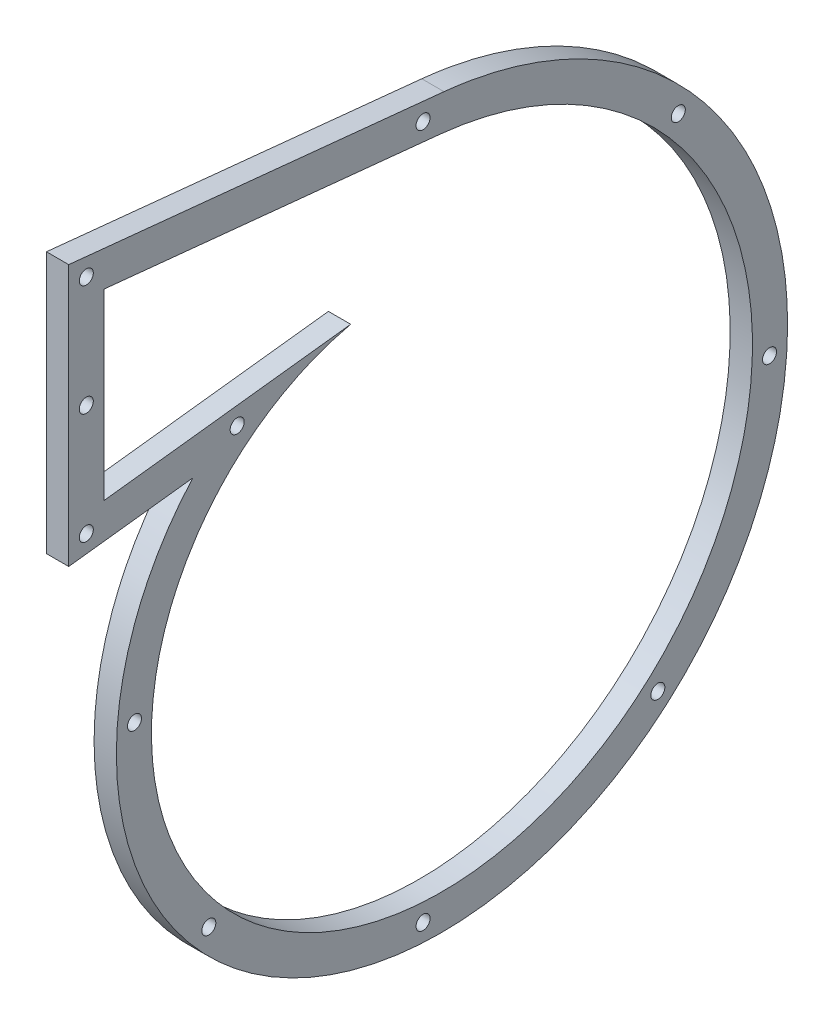
SolidWorks part; units mm, degrees
ref_plane "Front Plane" through (0, 0, 0) normal (0, 0, 1) x (1, 0, 0)
ref_plane "Top Plane" through (0, 0, 0) normal (0, 1, 0) x (1, 0, 0)
ref_plane "Right Plane" through (0, 0, 0) normal (1, 0, 0) x (0, 0, -1)
sketch "Sketch8" plane through (0, 0, 0) normal (1, 0, 0) x (0, 0, -1)
  line L0 (-42.4775, -245.3976) -> (306.8559, -245.3976) construction
  line L1 (-69, 0) -> (69, 0) construction
  circle A0 centre (0, 0) radius 69 construction
  point P15 (-130.5969, 140.8094)
  dimension "D1" = 138
sketch "Sketch4" plane through (0, 0, 0) normal (1, 0, 0) x (0, 0, -1)
  circle A0 centre (0, 0) radius 70.5
  dimension "D1" = 141
curve "Helix/Spiral1"
sketch "Sketch10" plane through (0, 0, 0) normal (1, 0, 0) x (0, 0, -1)
  line L0 (-20.6122, 67.4195) -> (-90.9357, 59.067)
  line L1 (-90.9357, 59.067) -> (-90.9357, 111.2319)
  line L2 (-90.9357, 111.2319) -> (4.9673, 101.5636)
  line L3 (-65.5693, 52.0095) -> (-100.9357, 47.809)
  line L4 (-100.9357, 47.809) -> (-100.9357, 122.2908)
  line L5 (-100.9357, 122.2908) -> (5.9703, 111.5132)
  line L6 (-95.9357, 116.7613) -> (5.4688, 106.5384) construction
  line L7 (-50.784, 58.8008) -> (-95.9357, 53.438) construction
  line L8 (-95.9357, 53.438) -> (-95.9357, 116.7613) construction
  spline S0 degree 3 poles (-1473.523, -1263.5766) (345.358, -198.0387) (91.6406, 117.3978) (-37.2156, 61.5605) (-41.1456, 59.4055) (-48.5847, 54.3658) (-52.0936, 51.4811) (-58.5545, 45.0647) (-61.5064, 41.533) (-66.7338, 33.9308) (-69.0091, 29.8604) (-72.7852, 21.311) (-74.2858, 16.8321) (-76.4391, 7.6138) (-77.0917, 2.8745) (-77.5044, -6.7034) (-77.2643, -11.5418) (-75.8778, -21.1493) (-74.7312, -25.9181) (-71.5495, -35.2161) (-69.5143, -39.7451) (-64.6057, -48.3972) (-61.7322, -52.5202) (-55.2279, -60.2051) (-51.5972, -63.7667) (-43.6886, -70.1896) (-39.4108, -73.0506) (-30.3435, -77.9547) (-25.5542, -79.9976) (-15.621, -83.1743) (-10.4772, -84.3079) (-0.0081, -85.6048) (5.317, -85.7681) (15.9653, -85.0965) (21.2883, -84.2616) (31.7447, -81.6003) (36.878, -79.774) (46.77, -75.1721) (51.5286, -72.3965) (60.4956, -65.9727) (64.7037, -62.3246) (72.4098, -54.265) (75.9074, -49.8536) (82.0541, -40.406) (84.7029, -35.3699) (89.0406, -24.8366) (90.7293, -19.3395) (93.067, -8.0675) (93.7159, -2.2928) (93.9294, 9.3374) (93.494, 15.1928) (91.5315, 26.7803) (90.0045, 32.5123) (85.8901, 43.6496) (83.3027, 49.0546) (77.1367, 59.3415) (73.5582, 64.2232) (65.5155, 73.2817) (61.0515, 77.4583) (51.3765, 84.9462) (46.1658, 88.2572) (35.1654, 93.8808) (29.376, 96.1932) (-135.5849, 144.7956) (-431.1519, -196.4432) (1091.6477, -1521.9747) knots -0.92756 -0.92756 -0.92756 -0.92756 0.03125 0.03125 0.0625 0.0625 0.09375 0.09375 0.125 0.125 0.15625 0.15625 0.1875 0.1875 0.21875 0.21875 0.25 0.25 0.28125 0.28125 0.3125 0.3125 0.34375 0.34375 0.375 0.375 0.40625 0.40625 0.4375 0.4375 0.46875 0.46875 0.5 0.5 0.53125 0.53125 0.5625 0.5625 0.59375 0.59375 0.625 0.625 0.65625 0.65625 0.6875 0.6875 0.71875 0.71875 0.75 0.75 0.78125 0.78125 0.8125 0.8125 0.84375 0.84375 0.875 0.875 0.90625 0.90625 0.9375 0.9375 0.96875 0.96875 1.799093 1.799093 1.799093 1.799093 only from (-20.6122, 67.4195) to (4.9673, 101.5636) construction
  spline S1 degree 3 poles (-20.6122, 67.4195) (-24.8771, 66.4553) (-29.0812, 65.0854) (-37.2156, 61.5605) (-41.1456, 59.4055) (-48.5847, 54.3658) (-52.0936, 51.4811) (-58.5545, 45.0647) (-61.5064, 41.533) (-66.7338, 33.9308) (-69.0091, 29.8604) (-72.7852, 21.311) (-74.2858, 16.8321) (-76.4391, 7.6138) (-77.0917, 2.8745) (-77.5044, -6.7034) (-77.2643, -11.5418) (-75.8778, -21.1493) (-74.7312, -25.9181) (-71.5495, -35.2161) (-69.5143, -39.7451) (-64.6057, -48.3972) (-61.7322, -52.5202) (-55.2279, -60.2051) (-51.5972, -63.7667) (-43.6886, -70.1896) (-39.4108, -73.0506) (-30.3435, -77.9547) (-25.5542, -79.9976) (-15.621, -83.1743) (-10.4772, -84.3079) (-0.0081, -85.6048) (5.317, -85.7681) (15.9653, -85.0965) (21.2883, -84.2616) (31.7447, -81.6003) (36.878, -79.774) (46.77, -75.1721) (51.5286, -72.3965) (60.4956, -65.9727) (64.7037, -62.3246) (72.4098, -54.265) (75.9074, -49.8536) (82.0541, -40.406) (84.7029, -35.3699) (89.0406, -24.8366) (90.7293, -19.3395) (93.067, -8.0675) (93.7159, -2.2928) (93.9294, 9.3374) (93.494, 15.1928) (91.5315, 26.7803) (90.0045, 32.5123) (85.8901, 43.6496) (83.3027, 49.0546) (77.1367, 59.3415) (73.5582, 64.2232) (65.5155, 73.2817) (61.0515, 77.4583) (51.3765, 84.9462) (46.1658, 88.2572) (35.1654, 93.8808) (29.376, 96.1932) (17.4097, 99.7188) (11.2331, 100.9319) (4.9673, 101.5636) knots 0 0 0 0 0.03125 0.03125 0.0625 0.0625 0.09375 0.09375 0.125 0.125 0.15625 0.15625 0.1875 0.1875 0.21875 0.21875 0.25 0.25 0.28125 0.28125 0.3125 0.3125 0.34375 0.34375 0.375 0.375 0.40625 0.40625 0.4375 0.4375 0.46875 0.46875 0.5 0.5 0.53125 0.53125 0.5625 0.5625 0.59375 0.59375 0.625 0.625 0.65625 0.65625 0.6875 0.6875 0.71875 0.71875 0.75 0.75 0.78125 0.78125 0.8125 0.8125 0.84375 0.84375 0.875 0.875 0.90625 0.90625 0.9375 0.9375 0.96875 0.96875 1 1 1 1
  spline S2 degree 1 poles (-65.5693, 52.0095) (5.9703, 111.5132) knots 0 0 1 1 construction
  spline S3 degree 3 poles (5.9703, 111.5132) (9.0502, 111.2027) (15.1958, 110.3222) (27.2245, 107.5606) (41.6726, 102.2691) (57.5832, 93.2003) (76.3494, 77.8774) (94.2744, 53.5338) (104.8435, 19.4438) (103.6779, -15.6365) (91.2896, -47.8483) (69.4058, -73.7703) (40.739, -90.7848) (8.6549, -97.3414) (-23.2206, -93.0918) (-51.4146, -78.887) (-72.9798, -56.6412) (-85.8046, -29.0853) (-88.8163, 0.5711) (-83.1915, 24.2521) (-74.3664, 41.0756) (-68.6986, 48.5351) (-65.5693, 52.0095) knots 0.103071 0.103071 0.103071 0.103071 0.117086 0.1311 0.159129 0.187158 0.215187 0.271245 0.327303 0.383361 0.439419 0.495478 0.551536 0.607594 0.663652 0.71971 0.775768 0.831826 0.887884 0.943942 0.971971 1 1 1 1
  spline S4 degree 1 poles (-50.784, 58.8008) (5.4688, 106.5384) knots 0 0 1 1 construction
  spline S5 degree 3 poles (5.4688, 106.5384) (8.5159, 106.2312) (14.596, 105.3508) (26.4818, 102.5654) (40.7204, 97.2041) (56.3054, 88.0071) (74.5135, 72.4897) (91.4744, 47.9359) (100.4641, 13.9232) (97.446, -20.4914) (83.2016, -51.2696) (59.808, -74.9425) (30.3424, -89.0046) (-1.5174, -92.1742) (-31.9496, -84.5006) (-57.4478, -67.3086) (-75.2244, -42.9932) (-83.5129, -14.694) (-81.7407, 14.1082) (-72.405, 35.6955) (-62.5096, 48.2726) (-56.0434, 54.6019) (-52.5779, 57.4513) (-50.784, 58.8008) knots 0.070786 0.070786 0.070786 0.070786 0.085305 0.099824 0.128862 0.1579 0.186938 0.245014 0.303089 0.361165 0.419241 0.477317 0.535393 0.593469 0.651545 0.709621 0.767696 0.825772 0.883848 0.941924 0.970962 0.985481 1 1 1 1 construction
  dimension "D1" = 10
  dimension "D2" = 5
extrude "Boss-Extrude1" add sketch "Sketch10" along normal blind 6.35
sketch "Sketch11" plane through (6.35, 0, 0) normal (1, 0, 0) x (0, 0, -1)
  line L0 (-61.04, -61.04) -> (72.7052, 72.7052) construction
  line L1 (-69, 0) -> (69, 0) construction
  line L2 (66.8741, -66.8741) -> (-55.6034, 55.6034) construction
  line L13 (-95.9357, 53.438) -> (-52.9561, 58.5428) construction
  line L14 (-95.9357, 116.7613) -> (-95.9357, 53.438) construction
  line L15 (5.4688, 106.5384) -> (-95.9357, 116.7613) construction
  circle A0 centre (-95.9357, 116.7613) radius 2
  circle A1 centre (-95.9357, 53.438) radius 2
  circle A2 centre (-95.9357, 85.0997) radius 2
  circle A3 centre (-52.9561, 58.5428) radius 2
  circle A4 centre (0, -90.449) radius 2
  circle A5 centre (-82.2025, 0) radius 2
  circle A6 centre (98.6959, 0) radius 2
  circle A7 centre (0, 107.0897) radius 2
  circle A8 centre (-61.04, -61.04) radius 2
  circle A9 centre (66.8741, -66.8741) radius 2
  circle A10 centre (72.7052, 72.7052) radius 2
  spline S4 degree 3 poles (-52.9561, 58.5428) (-54.7121, 56.5931) (-57.3462, 53.6685) (-59.9802, 50.7439) (-61.2972, 49.2816) (-61.7383, 48.7957) (-62.6098, 47.8162) (-63.0388, 47.3217) (-66.8402, 42.8287) (-69.7954, 38.5343) (-73.5979, 31.6459) (-74.7599, 29.275) (-76.0735, 26.2128) (-76.3296, 25.5943) (-76.8254, 24.3536) (-77.0649, 23.7314) (-77.7592, 21.8594) (-78.1895, 20.6042) (-79.3851, 16.8174) (-80.0554, 14.2648) (-81.1472, 9.1044) (-81.5687, 6.4966) (-82.0109, 2.5428) (-82.1266, 1.2178) (-82.2513, -0.7804) (-82.2847, -1.4491) (-82.3351, -2.7835) (-82.3521, -3.4496) (-82.3964, -6.7758) (-82.3028, -9.4215) (-81.8667, -14.6836) (-81.5242, -17.3) (-80.5901, -22.5034) (-79.9985, -25.0904) (-78.9172, -28.948) (-78.5252, -30.2266) (-77.6853, -32.7504) (-77.2366, -33.9985) (-75.8064, -37.7023) (-74.7408, -40.1175) (-72.3894, -44.842) (-71.1036, -47.1513) (-69.0064, -50.5342) (-68.2793, -51.6483) (-66.7674, -53.8489) (-65.984, -54.9332) (-63.5722, -58.1124) (-61.8755, -60.1443) (-58.3108, -64.0389) (-56.4427, -65.9017) (-52.5356, -69.4584) (-50.4964, -71.1524) (-47.3052, -73.5626) (-46.2179, -74.3448) (-44.0208, -75.8499) (-42.9085, -76.5749) (-37.2801, -80.0651) (-32.5652, -82.4306) (-26.4093, -84.8606) (-25.1649, -85.32) (-22.6491, -86.1847) (-21.3747, -86.5907) (-17.5336, -87.719) (-14.957, -88.3503) (-7.1814, -89.8977) (-1.9372, -90.4707) (4.6942, -90.61) (6.0243, -90.6087) (8.6924, -90.5467) (10.028, -90.4858) (14.0085, -90.2161) (16.6387, -89.9208) (24.4618, -88.7007) (29.5877, -87.4449) (35.8811, -85.3118) (37.136, -84.856) (39.6252, -83.8895) (40.8548, -83.3808) (44.5001, -81.7804) (46.8722, -80.6144) (53.8199, -76.8289) (58.2283, -73.9243) (63.4521, -69.8046) (64.4847, -68.9538) (66.5054, -67.2151) (67.4938, -66.3269) (70.3953, -63.6076) (72.2445, -61.7216) (77.544, -55.8507) (80.7485, -51.6547) (84.3312, -46.0467) (85.0278, -44.9043) (86.3666, -42.6009) (87.0098, -41.4388) (88.8624, -37.922) (89.9952, -35.5368) (93.0954, -28.2626) (94.7669, -23.256) (96.3486, -16.7959) (96.6399, -15.4907) (97.1665, -12.8782) (97.402, -11.5707) (98.0273, -7.6442) (98.3359, -5.0214) (98.9465, 2.8618) (98.9358, 8.137) (98.3887, 14.7563) (98.2522, 16.0832) (97.9251, 18.7315) (97.7353, 20.048) (97.0884, 23.9748) (96.5545, 26.5627) (94.6542, 34.2394) (92.9919, 39.2416) (90.4129, 45.3482) (89.8718, 46.5621) (88.7383, 48.975) (88.1463, 50.1723) (86.3087, 53.7106) (84.9968, 56.0081) (80.8107, 62.7235) (77.6878, 66.9655) (73.3692, 71.9747) (72.4845, 72.9617) (70.6728, 74.9058) (69.7438, 75.8647) (66.906, 78.6814) (64.9525, 80.4737) (58.9142, 85.6035) (54.6527, 88.6955) (47.9102, 92.8468) (45.6041, 94.1492) (42.0552, 95.9781) (40.8555, 96.5675) (38.4467, 97.6944) (37.2352, 98.2332) (31.1431, 100.8061) (26.1593, 102.4801) (15.977, 105.0783) (10.7787, 106.0031) (5.4688, 106.5384) knots 0 0 0 0 0.015625 0.023438 0.023438 0.027344 0.027344 0.03125 0.03125 0.0625 0.0625 0.078125 0.078125 0.082031 0.082031 0.085937 0.085937 0.09375 0.09375 0.109375 0.109375 0.125 0.125 0.132812 0.132812 0.136719 0.136719 0.140625 0.140625 0.15625 0.15625 0.171875 0.171875 0.1875 0.1875 0.195312 0.195312 0.203125 0.203125 0.21875 0.21875 0.234375 0.234375 0.242187 0.242187 0.25 0.25 0.265625 0.265625 0.28125 0.28125 0.296875 0.296875 0.304687 0.304687 0.3125 0.3125 0.34375 0.34375 0.351562 0.351562 0.359375 0.359375 0.375 0.375 0.40625 0.40625 0.414062 0.414062 0.421875 0.421875 0.4375 0.4375 0.46875 0.46875 0.476562 0.476562 0.484375 0.484375 0.5 0.5 0.53125 0.53125 0.539062 0.539062 0.546875 0.546875 0.5625 0.5625 0.59375 0.59375 0.601562 0.601562 0.609375 0.609375 0.625 0.625 0.65625 0.65625 0.664062 0.664062 0.671875 0.671875 0.6875 0.6875 0.71875 0.71875 0.726563 0.726563 0.734375 0.734375 0.75 0.75 0.78125 0.78125 0.789063 0.789063 0.796875 0.796875 0.8125 0.8125 0.84375 0.84375 0.851562 0.851562 0.859375 0.859375 0.875 0.875 0.90625 0.90625 0.921875 0.921875 0.929687 0.929687 0.9375 0.9375 0.96875 0.96875 1 1 1 1 construction
  dimension "D4" = 4
  dimension "D5" = 4
  dimension "D6" = 4
  dimension "D7" = 4
  dimension "D8" = 4
  dimension "D9" = 4
  dimension "D10" = 4
  dimension "D11" = 4
  dimension "D12" = 4
  dimension "D13" = 4
  dimension "D14" = 4
  dimension "D2" = 45
  dimension "D3" = 45
extrude "Cut-Extrude2" cut sketch "Sketch11" against normal blind 10
